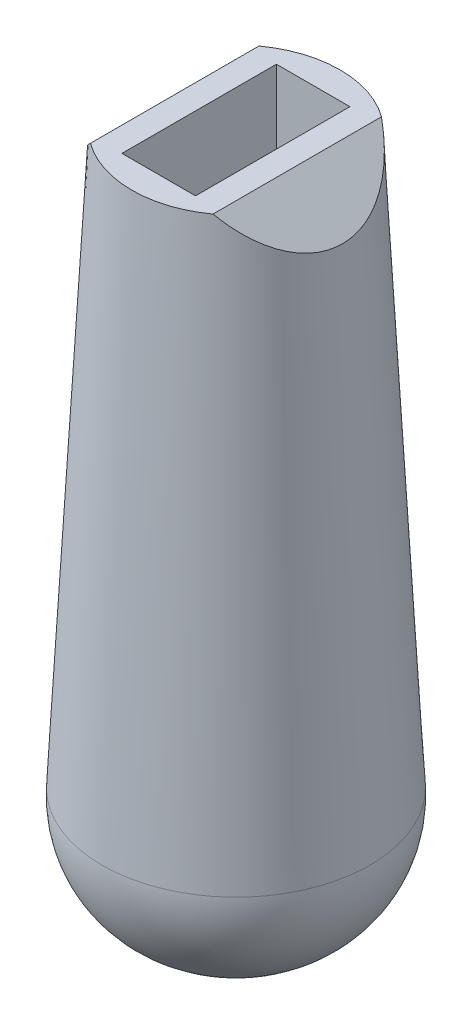
SolidWorks part; units mm, degrees
ref_plane "Front Plane" through (0, 0, 0) normal (0, 0, 1) x (1, 0, 0)
ref_plane "Top Plane" through (0, 0, 0) normal (0, 1, 0) x (1, 0, 0)
ref_plane "Right Plane" through (0, 0, 0) normal (1, 0, 0) x (0, 0, -1)
sketch "Sketch1" plane through (0, 0, 0) normal (0, 1, 0) x (1, 0, 0)
  circle A0 centre (0, 0) radius 8.5
  dimension "D1" = 17
extrude "Boss-Extrude1" add sketch "Sketch1" against normal blind 57 draft 3 draft outward yes
fillet "Fillet1" radius 10 1 edges at (0, -57, 11.4872)
sketch "Sketch2" plane through (0, 0, 0) normal (1, 0, 0) x (0, 0, -1)
  line L0 (8.5, 0) -> (-8.5, 0) construction
  line L1 (-6.3, 0) -> (6.3, 0)
  line L2 (-6.3, 0) -> (-6.3, -46.4766)
  line L3 (-6.3, -46.4766) -> (6.3, -46.4766) construction
  line L4 (6.3, 0) -> (6.3, -46.4766)
  line L5 (10.9357, -46.4766) -> (-10.9357, -46.4766) construction
  arc A0 (-6.3, -46.4766) -> (6.3, -46.4766) centre (0, -46.4766) ccw
  point P8 (0, 0)
  dimension "D1" = 12.6
extrude "Cut-Extrude1" cut sketch "Sketch2" against normal mid plane 6
sketch "Sketch3" plane through (0, 0, 0) normal (0, 0, 1) x (1, 0, 0)
  line L0 (-5, 0) -> (5, 0)
  line L1 (8.5, 0) -> (-8.5, 0) construction
  line L2 (5, 0) -> (10, -5)
  line L3 (10, -5) -> (10, 5)
  line L4 (10, 5) -> (-10, 5)
  line L5 (-10, 5) -> (-10, -5)
  line L6 (-10, -5) -> (-5, 0)
  point P4 (0, 0)
  dimension "D1" = 45
  dimension "D2" = 45
  dimension "D3" = 20
  dimension "D4" = 10
  dimension "D5" = 10
extrude "Cut-Extrude2" cut sketch "Sketch3" against normal mid plane 46
